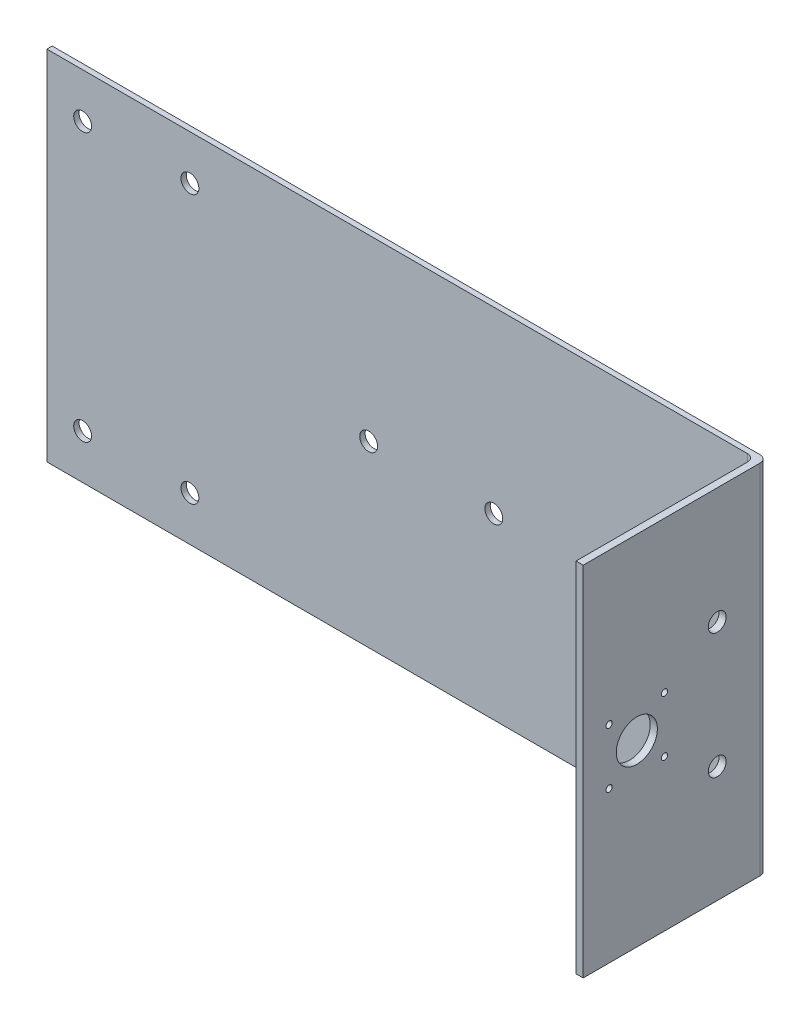
SolidWorks part; units mm, degrees
ref_plane "Front Plane" through (0, 0, 0) normal (0, 0, 1) x (1, 0, 0)
ref_plane "Top Plane" through (0, 0, 0) normal (0, 1, 0) x (1, 0, 0)
ref_plane "Right Plane" through (0, 0, 0) normal (1, 0, 0) x (0, 0, -1)
sketch "Sketch1" plane through (0, 0, 0) normal (0, 0, 1) x (1, 0, 0)
  line L1 (200, -100) -> (-200, -100)
  line L2 (200, -100) -> (200, 100)
  line L3 (200, 100) -> (-200, 100)
  line L4 (-200, -100) -> (-200, 100)
  line L5 (200, -100) -> (-200, 100) construction
  line L6 (200, 100) -> (-200, -100) construction
  point P0 (0, 0)
  dimension "D1" = 400
  dimension "D2" = 200
extrude "Boss-Extrude1" add sketch "Sketch1" along normal blind 3
sketch "Sketch2" plane through (0, 0, 0) normal (0, 0, -1) x (-1, 0, 0)
  line L0 (-200, 0) -> (-175, 0) construction
  line L1 (-200, -100) -> (-200, 100) construction
  line L2 (-175, 0) -> (-175, -50) construction
  line L3 (-175, -50) -> (-120, -50) construction
  line L4 (-120, -50) -> (-50, -50) construction
  line L5 (-50, -50) -> (20, -50) construction
  line L6 (70, -50) -> (75, -50) construction
  line L7 (200, -100) -> (-200, -100) construction
  line L8 (-175, 0) -> (97.2193, 0) construction
  line L9 (200, 100) -> (200, -100) construction
  line L10 (200, -100) -> (-200, -100) construction
  circle A10 centre (-120, 0) radius 5
  circle A11 centre (-50, 0) radius 5
  circle A12 centre (20, 0) radius 5
  circle A13 centre (180, -75) radius 5
  circle A14 centre (120, -75) radius 5
  circle A15 centre (120, 75) radius 5
  circle A16 centre (180, 75) radius 5
  dimension "D9" = 25
  dimension "D10" = 10
  dimension "D11" = 60
  dimension "D12" = 10
  dimension "D1" = 25
  dimension "D2" = 50
  dimension "D3" = 55
  dimension "D4" = 70
  dimension "D5" = 70
  dimension "D6" = 55
  dimension "D8" = 20
extrude "Cut-Extrude1" cut sketch "Sketch2" against normal blind 10
sketch "Sketch3" plane through (0, 0, 3) normal (0, 0, 1) x (1, 0, 0)
  line L0 (-200, -100) -> (200, -100) construction
  line L6 (200, 100) -> (196, 100)
  line L7 (200, 100) -> (200, -100)
  line L8 (200, -100) -> (196, -100)
  line L9 (196, 100) -> (196, -100)
  dimension "D2" = 4
extrude "Boss-Extrude2" add sketch "Sketch3" along normal blind 90
fillet "Fillet2" radius 4 2 edges at (200, 0, 0) (196, 0, 3)
sketch "Sketch4" plane through (200, 0, 0) normal (1, 0, 0) x (0, 0, -1)
  line L0 (0, 0) -> (-73, 0) construction
  line L1 (-4, -100) -> (-4, 100) construction
  circle A0 centre (-73, 0) radius 11.5
  dimension "D2" = 23
  dimension "D1" = 69
extrude "Cut-Extrude2" cut sketch "Sketch4" against normal blind 90
sketch "Sketch5" plane through (200, 0, 0) normal (1, 0, 0) x (0, 0, -1)
  circle A0 centre (-57.5, 15.5) radius 1.75
  circle A1 centre (-57.5, -15.5) radius 1.75
  circle A2 centre (-88.5, -15.5) radius 1.75
  circle A3 centre (-88.5, 15.5) radius 1.75
  circle A4 centre (-73, 0) radius 11.5 construction
  dimension "D1" = 3.5
  dimension "D2" = 15.5
  dimension "D3" = 15.5
  dimension "D4" = 15.5
  dimension "D5" = 15.5
  dimension "D6" = 15.5
  dimension "D7" = 15.5
  dimension "D8" = 15.5
  dimension "D9" = 15.5
extrude "Cut-Extrude3" cut sketch "Sketch5" against normal blind 90
sketch "Sketch6" plane through (200, 0, 0) normal (1, 0, 0) x (0, 0, -1)
  line L2 (-28, 0) -> (-28, -35) construction
  line L4 (-3, -100) -> (-3, 100) construction
  circle A0 centre (-28, -35) radius 5
  circle A1 centre (-28, 35) radius 5
  dimension "D3" = 10
  dimension "D1" = 25
  dimension "D4" = 25
  dimension "D2" = 35
extrude "Cut-Extrude4" cut sketch "Sketch6" against normal blind 15
sketch "Sketch7" plane through (0, 0, 93) normal (0, 0, 1) x (1, 0, 0)
  line L1 (196, -100) -> (200, -100)
  line L2 (196, -100) -> (196, 100)
  line L3 (196, 100) -> (200, 100)
  line L4 (200, -100) -> (200, 100)
extrude "Boss-Extrude3" add sketch "Sketch7" along normal blind 10
